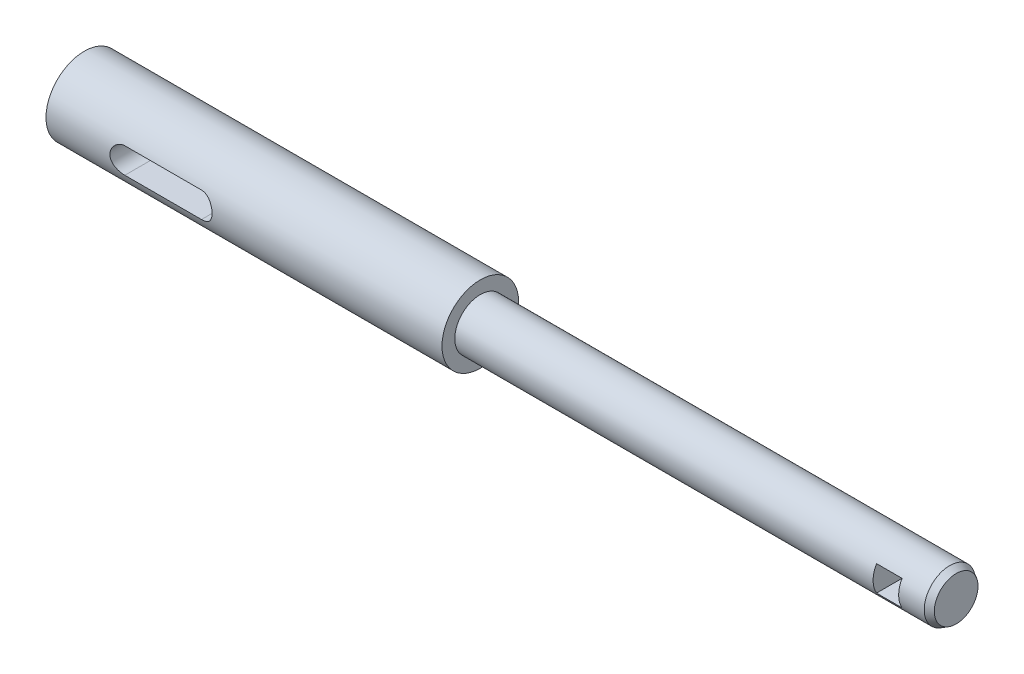
SolidWorks part; units mm, degrees
ref_plane "Front Plane" through (0, 0, 0) normal (0, 0, 1) x (1, 0, 0)
ref_plane "Top Plane" through (0, 0, 0) normal (0, 1, 0) x (1, 0, 0)
ref_plane "Right Plane" through (0, 0, 0) normal (1, 0, 0) x (0, 0, -1)
sketch "Sketch1" plane through (0, 0, 0) normal (0, 1, 0) x (1, 0, 0)
  line L0 (-31, 10.6429) -> (-31, -10.6429)
  line L1 (-31, -10.6429) -> (31, -10.6429)
  line L3 (31, 10.6429) -> (-31, 10.6429)
  line L4 (31, 0) -> (23.3254, 0) construction
  line L5 (31, 7.0952) -> (31, -7.0952)
  line L6 (31, 7.0952) -> (105.5, 7.0952)
  line L7 (31, -7.0952) -> (105.5, -7.0952)
  line L8 (105.5, -7.0952) -> (105.5, 7.0952)
  line L9 (31, 10.6429) -> (31, -10.6429)
  line L10 (-31, 0) -> (31, 0) construction
  point P7 (0, 0)
  point P10 (31, 0)
  point P13 (-31, 0)
  dimension "D1" = 74.5
  dimension "D2" = 21.2857
  dimension "D3" = 136.5
  dimension "D4" = 14.1905
extrude "Boss-Extrude1" add sketch "Sketch1" along normal blind 12 contours L9 L3 L0 L1
sketch "Sketch3" plane through (31, 0, 0) normal (1, 0, 0) x (0, 0, -1)
  line L0 (0, 0) -> (0, 12) construction
  line L3 (10.6429, 12) -> (-10.6429, 12) construction
  circle A0 centre (0, 6) radius 4
  point P6 (0, 6)
  dimension "D1" = 8
extrude "Boss-Extrude2" add sketch "Sketch3" along normal blind 74.5
sketch "Sketch4" plane through (-31, 0, 0) normal (-1, 0, 0) x (0, 0, 1)
  line L1 (10.6429, 0) -> (10.6429, 12) construction
  circle A1 centre (0, 6) radius 6
  dimension "D1" = 12
  dimension "D2" = 12
extrude "Cut-Extrude2" cut sketch "Sketch4" against normal through all flip side to cut
sketch "Sketch5" plane through (0, 0, 0) normal (0, 0, 1) x (1, 0, 0)
  line L0 (-31, 6) -> (105.5, 6) construction
  line L1 (-31, 12) -> (-31, 0) construction
  line L2 (105.5, 2) -> (105.5, 10) construction
  line L3 (-19, 6) -> (-7, 6) construction
  line L4 (-19, 8) -> (-7, 8)
  line L5 (-19, 4) -> (-7, 4)
  line L7 (96.5, 8) -> (100.5, 8)
  line L8 (96.5, 8) -> (96.5, 4)
  line L9 (96.5, 4) -> (100.5, 4)
  line L10 (100.5, 8) -> (100.5, 4)
  line L11 (96.5, 8) -> (100.5, 4) construction
  line L12 (96.5, 4) -> (100.5, 8) construction
  arc A0 (-19, 8) -> (-19, 4) centre (-19, 6) ccw
  arc A1 (-7, 4) -> (-7, 8) centre (-7, 6) ccw
  point P8 (-13, 6)
  point P13 (-21, 6)
  point P14 (98.5, 6)
  dimension "D1" = 10
  dimension "D2" = 12
  dimension "D3" = 4
  dimension "D4" = 5
  dimension "D5" = 4
  dimension "D6" = 4
extrude "Cut-Extrude3" cut sketch "Sketch5" against normal through all both and the other way through all
chamfer "Chamfer1" distance 1 angle 30 1 edges at (105.5, 6, -4)
